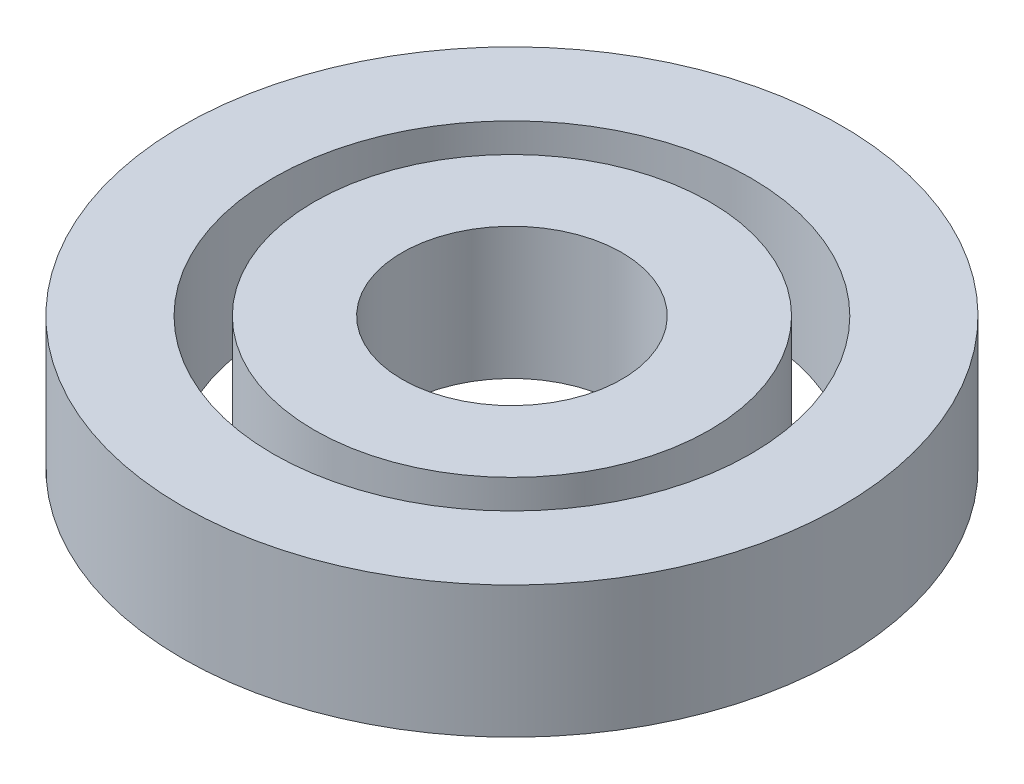
SolidWorks part; units mm, degrees
ref_plane "Front Plane" through (0, 0, 0) normal (0, 0, 1) x (1, 0, 0)
ref_plane "Top Plane" through (0, 0, 0) normal (0, 1, 0) x (1, 0, 0)
ref_plane "Right Plane" through (0, 0, 0) normal (1, 0, 0) x (0, 0, -1)
sketch "Sketch1" plane through (0, 0, 0) normal (0, 1, 0) x (1, 0, 0)
  circle A0 centre (0, 0) radius 10
  circle A1 centre (0, 0) radius 18
  dimension "D1" = 20
  dimension "D2" = 36
extrude "Boss-Extrude1" add sketch "Sketch1" along normal blind 12
sketch "Sketch2" plane through (0, 0, 0) normal (0, 1, 0) x (1, 0, 0)
  circle A0 centre (0, 0) radius 21.75
  circle A1 centre (0, 0) radius 30
  dimension "D1" = 43.5
  dimension "D2" = 60
extrude "Boss-Extrude2" add sketch "Sketch2" along normal blind 12 separate body
